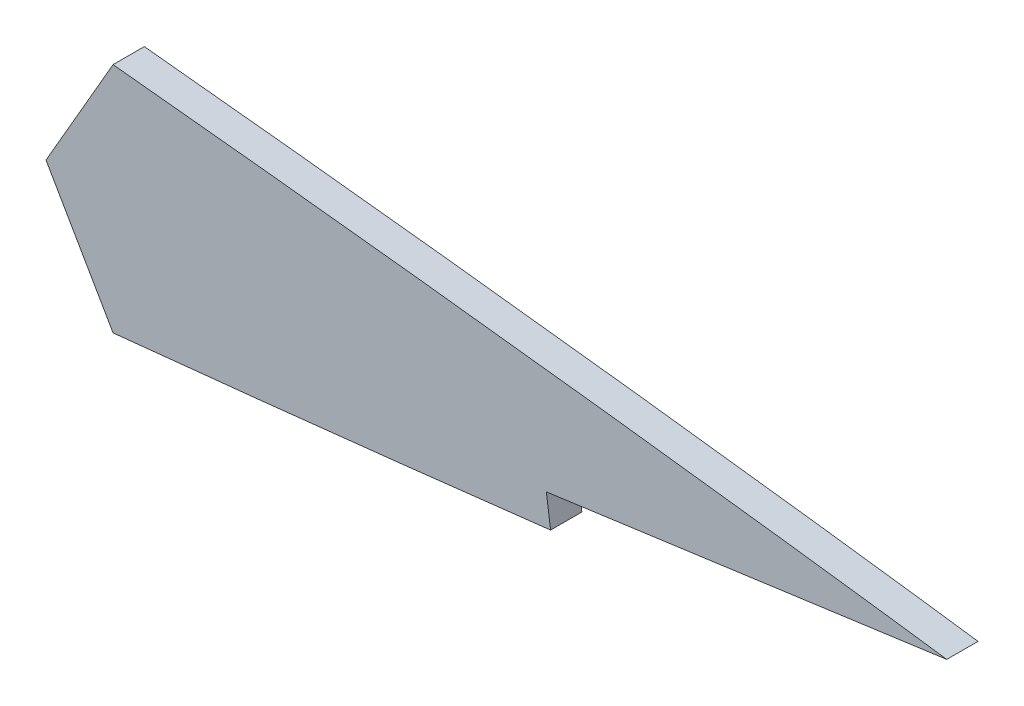
SolidWorks part; units mm, degrees
material "Plywood"
ref_plane "Front Plane" through (0, 0, 0) normal (0, 0, 1) x (1, 0, 0)
ref_plane "Top Plane" through (0, 0, 0) normal (0, 1, 0) x (1, 0, 0)
ref_plane "Right Plane" through (0, 0, 0) normal (1, 0, 0) x (0, 0, -1)
curve "Curve1"
  spline degree 3 poles (318.77, 0, 0) (318.6165, 0.178, 0) (318.1279, 0.7447, 0) (316.4159, 0.5798, 0) (314.0794, 1.1239, 0) (310.6457, 1.4976, 0) (306.3402, 2.1168, 0) (301.1057, 2.7975, 0) (295.0055, 3.5941, 0) (288.0665, 4.472, 0) (280.335, 5.4268, 0) (271.8575, 6.4421, 0) (262.6867, 7.5062, 0) (252.8789, 8.6045, 0) (242.4947, 9.7236, 0) (231.5982, 10.8496, 0) (220.2564, 11.9679, 0) (208.5394, 13.0629, 0) (196.5193, 14.1202, 0) (184.2704, 15.122, 0) (171.8679, 16.0521, 0) (159.3884, 16.8933, 0) (146.9087, 17.6278, 0) (134.5058, 18.2372, 0) (122.2562, 18.7052, 0) (110.2351, 19.0165, 0) (98.5168, 19.156, 0) (87.1732, 19.1125, 0) (76.2743, 18.8777, 0) (65.8873, 18.4456, 0) (56.076, 17.8151, 0) (46.9007, 16.9881, 0) (38.4176, 15.971, 0) (30.6784, 14.7725, 0) (23.7299, 13.4051, 0) (17.6134, 11.8842, 0) (12.3615, 10.2248, 0) (8.0073, 8.4423, 0) (4.5466, 6.5486, 0) (2.0351, 4.5401, 0) (0.333, 2.3682, 0) (0.1059, 0.7528, 0) (0, 0, 0) knots 0 0 0 0 0.002092 0.00666 0.01424 0.024785 0.038227 0.054481 0.073445 0.094999 0.119006 0.145319 0.17377 0.204184 0.236371 0.270129 0.30525 0.341517 0.378701 0.416575 0.454902 0.493447 0.531971 0.570237 0.608013 0.645066 0.681178 0.71613 0.749718 0.781748 0.812037 0.840415 0.866732 0.890849 0.912652 0.932046 0.948973 0.963413 0.975421 0.985175 0.993091 1 1 1 1
sketch "Sketch2" plane through (0, 0, 0) normal (0, 0, 1) x (1, 0, 0)
  line L4 (0, 0) -> (349.25, 0) construction
  spline S1 degree 3 poles (349.25, 0) (349.0818, 0.195) (348.5465, 0.8159) (346.6708, 0.6353) (344.1109, 1.2313) (340.3489, 1.6408) (335.6317, 2.3192) (329.8967, 3.065) (323.2132, 3.9378) (315.6107, 4.8996) (307.1399, 5.9457) (297.8518, 7.058) (287.8042, 8.224) (277.0586, 9.4273) (265.6815, 10.6534) (253.743, 11.887) (241.3168, 13.1123) (228.4795, 14.3119) (215.31, 15.4703) (201.8899, 16.5679) (188.3015, 17.587) (174.6287, 18.5086) (160.9558, 19.3133) (147.3669, 19.981) (133.9461, 20.4937) (120.7755, 20.8348) (107.9367, 20.9876) (95.5085, 20.94) (83.5675, 20.6828) (72.1873, 20.2093) (61.4378, 19.5185) (51.3852, 18.6124) (42.091, 17.4981) (33.6118, 16.185) (25.9989, 14.6868) (19.2975, 13.0206) (13.5435, 11.2025) (8.7729, 9.2495) (4.9814, 7.1748) (2.2297, 4.9742) (0.3649, 2.5947) (0.116, 0.8248) (0, 0) knots 0 0 0 0 0.002092 0.00666 0.01424 0.024785 0.038227 0.054481 0.073445 0.094999 0.119006 0.145319 0.17377 0.204184 0.236371 0.270129 0.30525 0.341517 0.378701 0.416575 0.454902 0.493447 0.531971 0.570237 0.608013 0.645066 0.681178 0.71613 0.749718 0.781748 0.812037 0.840415 0.866732 0.890849 0.912652 0.932046 0.948973 0.963413 0.975421 0.985175 0.993091 1 1 1 1
  spline S2 degree 3 poles (349.25, 0) (349.0818, -0.195) (348.5465, -0.8159) (346.6708, -0.6353) (344.1109, -1.2313) (340.3489, -1.6408) (335.6317, -2.3192) (329.8967, -3.065) (323.2132, -3.9378) (315.6107, -4.8996) (307.1399, -5.9457) (297.8518, -7.058) (287.8042, -8.224) (277.0586, -9.4273) (265.6815, -10.6534) (253.743, -11.887) (241.3168, -13.1123) (228.4795, -14.3119) (215.31, -15.4703) (201.8899, -16.5679) (188.3015, -17.587) (174.6287, -18.5086) (160.9558, -19.3133) (147.3669, -19.981) (133.9461, -20.4937) (120.7755, -20.8348) (107.9367, -20.9876) (95.5085, -20.94) (83.5675, -20.6828) (72.1873, -20.2093) (61.4378, -19.5185) (51.3852, -18.6124) (42.091, -17.4981) (33.6118, -16.185) (25.9989, -14.6868) (19.2975, -13.0206) (13.5435, -11.2025) (8.7729, -9.2495) (4.9814, -7.1748) (2.2297, -4.9742) (0.3649, -2.5947) (0.116, -0.8248) (0, 0) knots 0 0 0 0 0.002092 0.00666 0.01424 0.024785 0.038227 0.054481 0.073445 0.094999 0.119006 0.145319 0.17377 0.204184 0.236371 0.270129 0.30525 0.341517 0.378701 0.416575 0.454902 0.493447 0.531971 0.570237 0.608013 0.645066 0.681178 0.71613 0.749718 0.781748 0.812037 0.840415 0.866732 0.890849 0.912652 0.932046 0.948973 0.963413 0.975421 0.985175 0.993091 1 1 1 1
  dimension "D1" = 349.25
extrude "Boss-Extrude1" add sketch "Sketch2" along normal blind 3.175
sketch "Sketch3" plane through (0, 0, 3.175) normal (0, 0, 1) x (1, 0, 0)
  line L0 (0, 0) -> (247.65, 0) construction
  line L12 (247.65, 12.4852) -> (247.65, -12.4852) construction
  line L15 (247.65, 50.8) -> (0, 50.8)
  line L16 (0, 50.8) -> (0, 0)
  line L17 (0, 0) -> (0, -50.8)
  line L18 (0, -50.8) -> (247.65, -50.8)
  line L24 (299.3571, -10.0708) -> (349.6828, -3.1454)
  line L25 (299.3571, -10.0708) -> (298.4914, -3.78)
  line L26 (349.6828, -3.1454) -> (348.8172, 3.1454)
  line L27 (298.4914, -3.78) -> (348.8172, 3.1454)
  line L28 (247.65, 0) -> (254.4653, -11.8044)
  line L29 (247.65, 0) -> (254.4653, 11.8044)
  line L30 (254.4653, -11.8044) -> (247.65, -50.8)
  line L31 (247.65, 50.8) -> (254.4653, 11.8044)
  spline S0 degree 3 poles (-1885.9182, -664.5546) (82.698, 68.0169) (-10.8809, 11.7551) (2.2297, -4.9742) (4.9814, -7.1748) (8.7729, -9.2495) (13.5435, -11.2025) (19.2975, -13.0206) (25.9989, -14.6868) (33.6118, -16.185) (42.091, -17.4981) (51.3852, -18.6124) (61.4378, -19.5185) (72.1873, -20.2093) (83.5675, -20.6828) (95.5085, -20.94) (107.9367, -20.9876) (120.7755, -20.8348) (133.9461, -20.4937) (147.3669, -19.981) (160.9558, -19.3133) (174.6287, -18.5086) (188.3015, -17.587) (201.8899, -16.5679) (215.31, -15.4703) (228.4795, -14.3119) (241.3168, -13.1123) (253.743, -11.887) (265.6815, -10.6534) (277.0586, -9.4273) (287.8042, -8.224) (297.8518, -7.058) (307.1399, -5.9457) (315.6107, -4.8996) (323.2132, -3.9378) (329.8967, -3.065) (335.6317, -2.3192) (340.3489, -1.6408) (344.1109, -1.2313) (346.6708, -0.6353) (356.7064, -1.6019) (329.4604, 72.3888) (1240.1965, -1790.0909) knots -0.148221 -0.148221 -0.148221 -0.148221 0.006909 0.014825 0.024579 0.036587 0.051027 0.067954 0.087348 0.109151 0.133268 0.159585 0.187963 0.218252 0.250282 0.28387 0.318822 0.354934 0.391987 0.429763 0.468029 0.506553 0.545098 0.583425 0.621299 0.658483 0.69475 0.729871 0.763629 0.795816 0.82623 0.854681 0.880994 0.905001 0.926555 0.945519 0.961773 0.975215 0.98576 0.99334 0.997908 1.061948 1.061948 1.061948 1.061948 only from (0, 0) to (349.25, 0) construction
  spline S1 degree 3 poles (1240.1982, 1790.0943) (329.4603, -72.3889) (356.7064, 1.6019) (346.6708, 0.6353) (344.1109, 1.2313) (340.3489, 1.6408) (335.6317, 2.3192) (329.8967, 3.065) (323.2132, 3.9378) (315.6107, 4.8996) (307.1399, 5.9457) (297.8518, 7.058) (287.8042, 8.224) (277.0586, 9.4273) (265.6815, 10.6534) (253.743, 11.887) (241.3168, 13.1123) (228.4795, 14.3119) (215.31, 15.4703) (201.8899, 16.5679) (188.3015, 17.587) (174.6287, 18.5086) (160.9558, 19.3133) (147.3669, 19.981) (133.9461, 20.4937) (120.7755, 20.8348) (107.9367, 20.9876) (95.5085, 20.94) (83.5675, 20.6828) (72.1873, 20.2093) (61.4378, 19.5185) (51.3852, 18.6124) (42.091, 17.4981) (33.6118, 16.185) (25.9989, 14.6868) (19.2975, 13.0206) (13.5435, 11.2025) (8.7729, 9.2495) (4.9814, 7.1748) (2.2297, 4.9742) (-10.8807, -11.7548) (82.6949, -68.015) (-1885.8156, 664.5164) knots -0.061948 -0.061948 -0.061948 -0.061948 0.002092 0.00666 0.01424 0.024785 0.038227 0.054481 0.073445 0.094999 0.119006 0.145319 0.17377 0.204184 0.236371 0.270129 0.30525 0.341517 0.378701 0.416575 0.454902 0.493447 0.531971 0.570237 0.608013 0.645066 0.681178 0.71613 0.749718 0.781748 0.812037 0.840415 0.866732 0.890849 0.912652 0.932046 0.948973 0.963413 0.975421 0.985175 0.993091 1.148218 1.148218 1.148218 1.148218 only from (349.25, 0) to (0, 0) construction
  spline S2 degree 3 poles (247.65, -12.4852) (249.7346, -12.2798) (255.8081, -11.6736) (265.6815, -10.6534) (277.0586, -9.4273) (287.8042, -8.224) (297.8518, -7.058) (307.1399, -5.9457) (315.6107, -4.8996) (323.2132, -3.9378) (329.8967, -3.065) (335.6317, -2.3192) (340.3489, -1.6408) (344.1109, -1.2313) (346.6708, -0.6353) (348.5465, -0.8159) (349.0818, -0.195) (349.25, 0) knots 0.712232 0.712232 0.712232 0.712232 0.729871 0.763629 0.795816 0.82623 0.854681 0.880994 0.905001 0.926555 0.945519 0.961773 0.975215 0.98576 0.99334 0.997908 1 1 1 1 construction
  spline S3 degree 3 poles (349.25, 0) (349.0818, 0.195) (348.5465, 0.8159) (346.6708, 0.6353) (344.1109, 1.2313) (340.3489, 1.6408) (335.6317, 2.3192) (329.8967, 3.065) (323.2132, 3.9378) (315.6107, 4.8996) (307.1399, 5.9457) (297.8518, 7.058) (287.8042, 8.224) (277.0586, 9.4273) (265.6815, 10.6534) (255.8081, 11.6736) (249.7346, 12.2798) (247.65, 12.4852) knots 0 0 0 0 0.002092 0.00666 0.01424 0.024785 0.038227 0.054481 0.073445 0.094999 0.119006 0.145319 0.17377 0.204184 0.236371 0.270129 0.287768 0.287768 0.287768 0.287768 construction
  point P3 (298.9243, -6.9254)
  dimension "D5" = 50.8
  dimension "D1" = 50.8
  dimension "D2" = 101.6
  dimension "D3" = 30
  dimension "D4" = 50.8
  dimension "D6" = 6.35
extrude "Cut-Extrude1" cut sketch "Sketch3" against normal blind 5.08
ref_plane "Adjusted Right Plane" through (247.65, 0, 0) normal (1, 0, 0) x (0, 0, -1)
